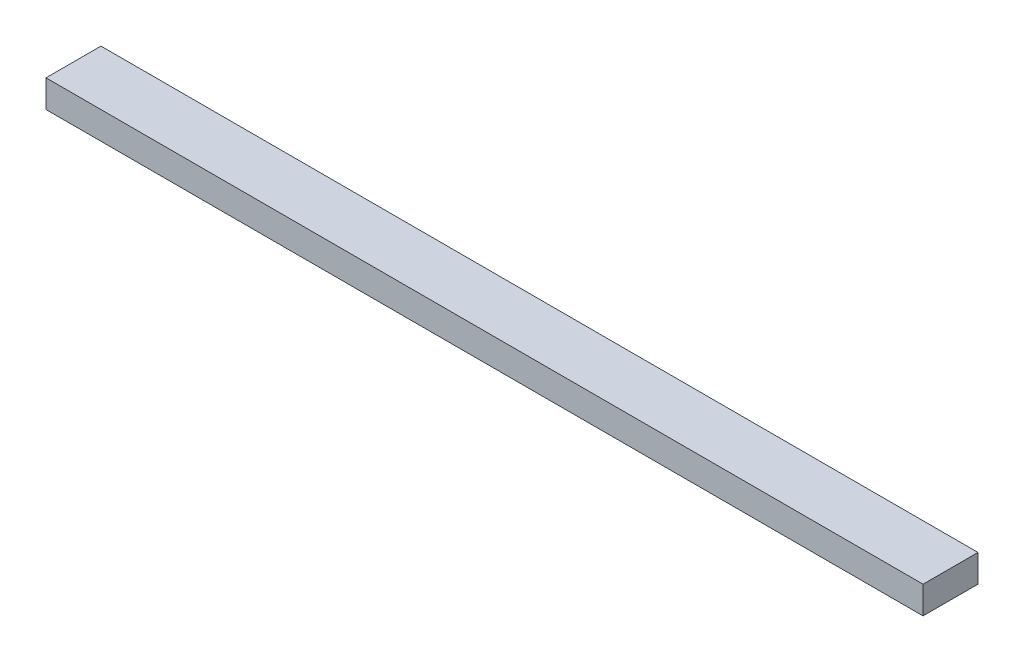
SolidWorks part; units mm, degrees
material "Pine"
ref_plane "Front Plane" through (0, 0, 0) normal (0, 0, 1) x (1, 0, 0)
ref_plane "Top Plane" through (0, 0, 0) normal (0, 1, 0) x (1, 0, 0)
ref_plane "Right Plane" through (0, 0, 0) normal (1, 0, 0) x (0, 0, -1)
sketch "Sketch1" plane through (0, 0, 0) normal (0, 1, 0) x (1, 0, 0)
  line L1 (0, 0) -> (608.0125, 0)
  line L2 (0, 0) -> (0, 38.1)
  line L3 (0, 38.1) -> (608.0125, 38.1)
  line L4 (608.0125, 0) -> (608.0125, 38.1)
  dimension "D1" = 38.1
  dimension "D2" = 608.0125
extrude "Boss-Extrude1" add sketch "Sketch1" along normal blind 19.05
